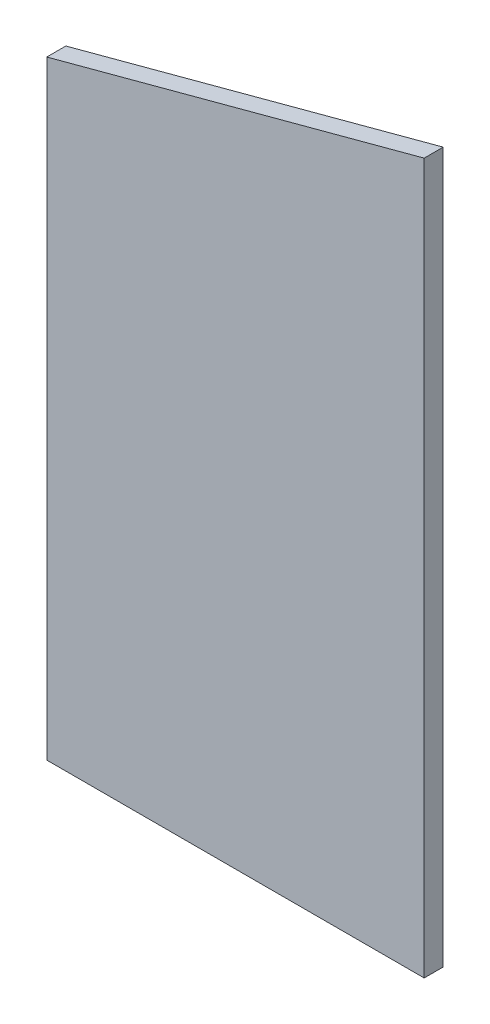
SolidWorks part; units mm, degrees
material "Pine"
ref_plane "Front Plane" through (0, 0, 0) normal (0, 0, 1) x (1, 0, 0)
ref_plane "Top Plane" through (0, 0, 0) normal (0, 1, 0) x (1, 0, 0)
ref_plane "Right Plane" through (0, 0, 0) normal (1, 0, 0) x (0, 0, -1)
sketch "Sketch1" plane through (0, 0, 0) normal (0, 0, 1) x (1, 0, 0)
  line L0 (-819.8306, 11.9062) -> (-819.8306, 392.5997)
  line L1 (-819.8306, 392.5997) -> (-583.9002, 455.817)
  line L2 (-583.9002, 455.817) -> (-583.9002, 11.9062)
  line L3 (-583.9002, 11.9062) -> (-819.8306, 11.9062)
  line L4 (-819.8306, 11.9062) -> (-583.9002, 11.9063) construction
  line L5 (-819.8306, 392.5997) -> (-819.8306, 11.9062) construction
  line L6 (-583.9002, 455.817) -> (-819.8306, 392.5997) construction
  line L7 (-583.9002, 11.9063) -> (-583.9002, 455.817) construction
extrude "Boss-Extrude1" add sketch "Sketch1" against normal up to surface (11.9063 mm away)
